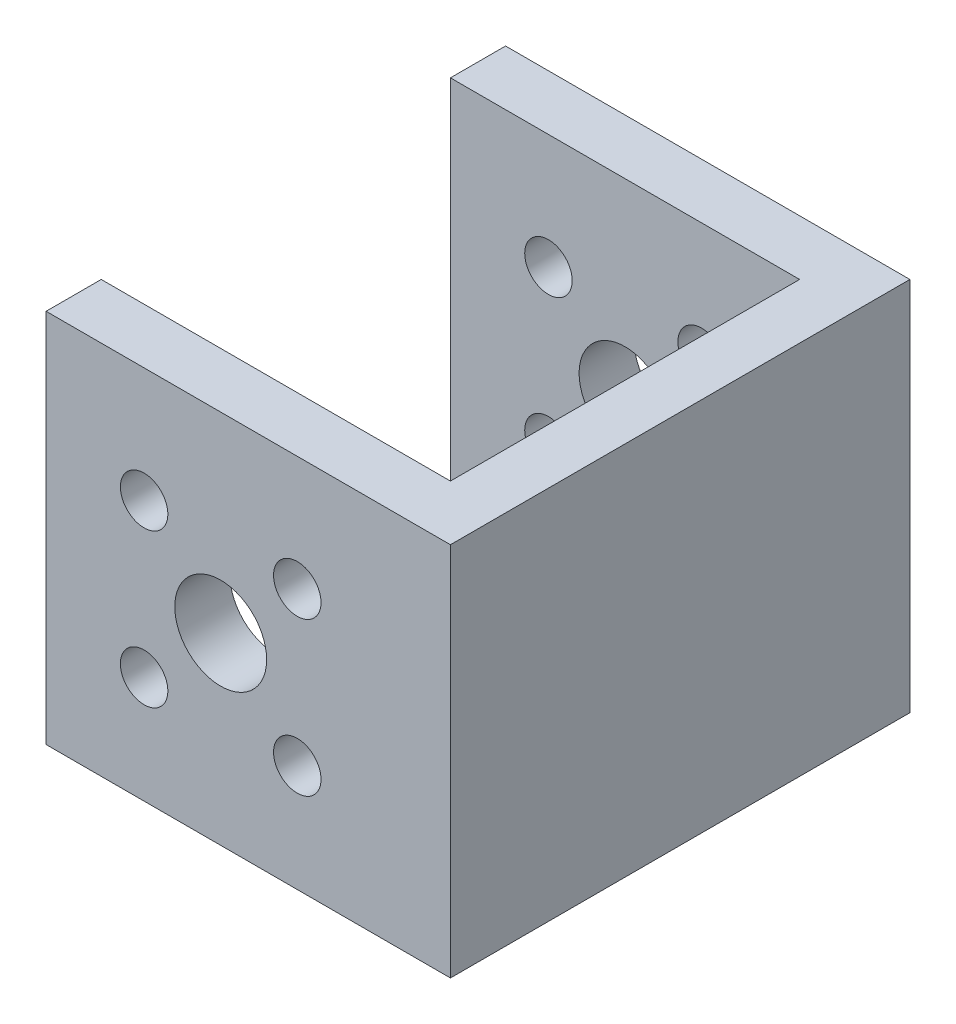
SolidWorks part; units mm, degrees
ref_plane "前视基准面" through (0, 0, 0) normal (0, 0, 1) x (1, 0, 0)
ref_plane "上视基准面" through (0, 0, 0) normal (0, 1, 0) x (1, 0, 0)
ref_plane "右视基准面" through (0, 0, 0) normal (1, 0, 0) x (0, 0, -1)
sketch "草图1" plane through (0, 0, 0) normal (0, 0, 1) x (1, 0, 0)
  line L1 (15, 0) -> (15, 12.5)
  line L2 (0, 12.5) -> (15, 12.5)
  line L3 (-15, 12.5) -> (-15, -24)
  line L4 (15, 0) -> (15, -24)
  line L5 (15, -24) -> (-15, -24)
  line L9 (0, 0) -> (0, -19) construction
  line L10 (-5, 0) -> (-5, -5) construction
  line L11 (-5, -5) -> (0, -5) construction
  line L12 (0, -5) -> (5, -5) construction
  line L13 (5, -5) -> (5, 5) construction
  line L14 (5, 5) -> (-5, 5) construction
  line L15 (-5, 5) -> (-5, 0) construction
  line L25 (0, 12.5) -> (-15, 12.5)
  circle A0 centre (0, 0) radius 3
  circle A1 centre (-5, 5) radius 1.55
  circle A2 centre (-5, -5) radius 1.55
  circle A3 centre (5, -5) radius 1.55
  circle A4 centre (5, 5) radius 1.55
extrude "凸台-拉伸1" add sketch "草图1" along normal blind 30
sketch "草图2" plane through (0, 12.5, 0) normal (0, 1, 0) x (1, 0, 0)
  line L0 (0, 0) -> (0, -30) construction
  line L1 (-15, 0) -> (15, 0) construction
  line L2 (-15, -30) -> (15, -30) construction
  line L3 (0, -30) -> (11.4, -30) construction
  line L4 (0, -30) -> (-11.1, -30) construction
  line L5 (-11.4, -15) -> (-11.4, -3.6)
  line L6 (-11.1, 0) -> (11.1, 0) construction
  line L7 (-11.4, -15) -> (-11.4, -26.4)
  line L8 (0, -26.4) -> (-11.4, -26.4)
  line L9 (11.4, -3.6) -> (11.4, -26.4)
  line L10 (0, -3.6) -> (11.4, -3.6)
  line L11 (11.4, -26.4) -> (0, -26.4)
  line L12 (0, -3.6) -> (-11.4, -3.6)
extrude "切除-拉伸1" cut sketch "草图2" against normal through all
sketch "草图4" plane through (0, -24, 0) normal (0, -1, 0) x (1, 0, 0)
  line L0 (-15, 0) -> (-15, 30)
  line L1 (-15, 30) -> (15, 30)
  line L2 (15, 30) -> (15, 0)
  line L3 (15, 0) -> (-15, 0)
extrude "切除-拉伸3" cut sketch "草图4" against normal blind 12
sketch "草图5" plane through (-15, 0, 0) normal (-1, 0, 0) x (0, 0, 1)
  line L0 (30, -12) -> (30, 11.5967)
  line L1 (30, -12) -> (0, -12)
  line L2 (0, -12) -> (0, 12.5)
  line L3 (0, 12.5) -> (30, 12.5)
  line L4 (30, 12.5) -> (30, 11.5967)
extrude "凸台-拉伸2" add sketch "草图5" along normal blind 55
sketch "草图6" plane through (0, 12.5, 0) normal (0, 1, 0) x (1, 0, 0)
  line L0 (-11.4, -3.6) -> (-11.4, 0)
  line L1 (-70, 0) -> (15, 0) construction
  line L2 (-11.4, -26.4) -> (-11.4, -30)
  line L3 (-70, -30) -> (15, -30) construction
  line L4 (-11.4, -30) -> (-70, -15)
  line L5 (-70, -30) -> (-70, 0) construction
  line L6 (-70, -15) -> (-11.4, 0)
  line L7 (-11.4, -3.6) -> (-11.4, -26.4)
  line L8 (-11.4, -15) -> (-56.4, -15) construction
  line L9 (-70, -15) -> (-70, 0)
  line L10 (-70, 0) -> (-11.4, 0)
  line L11 (-70, -15) -> (-70, -30)
  line L12 (-70, -30) -> (-11.4, -30)
  circle A0 centre (-56.4, -15) radius 2.3
  circle A1 centre (-33.9, -15) radius 5
  circle A2 centre (-22.1255, -15) radius 6
  circle A3 centre (-46.1105, -15) radius 4
extrude "切除-拉伸4" cut sketch "草图6" against normal through all
fillet "圆角2" radius 2 1 edges at (-70, 0.25, 15)
sketch "草图7" plane through (0, 12.5, 0) normal (0, 1, 0) x (1, 0, 0)
  line L0 (-11.4, -3.6) -> (-11.4, 0)
  line L1 (-11.4, 0) -> (-66.9549, 0)
  line L2 (-11.4, -30) -> (-66.4, -30)
  line L3 (-66.4, -30) -> (-66.9549, 0)
  line L4 (-11.4, -30) -> (-11.4, -3.6)
extrude "切除-拉伸5" cut sketch "草图7" against normal through all
